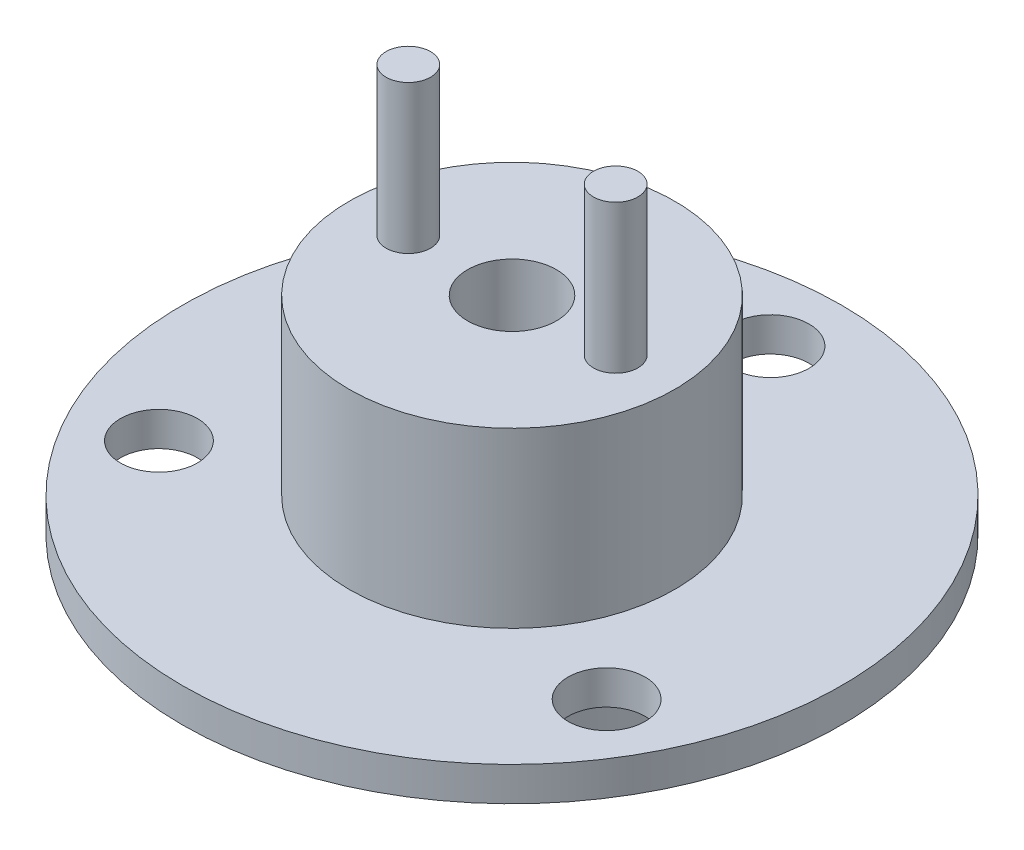
SolidWorks part; units mm, degrees
ref_plane "Alzado" through (0, 0, 0) normal (0, 0, 1) x (1, 0, 0)
ref_plane "Planta" through (0, 0, 0) normal (0, 1, 0) x (1, 0, 0)
ref_plane "Vista lateral" through (0, 0, 0) normal (1, 0, 0) x (0, 0, -1)
sketch "Croquis1" plane through (0, 0, 0) normal (0, 1, 0) x (1, 0, 0)
  circle A0 centre (0, 0) radius 11
  dimension "D1" = 22
extrude "Saliente-Extruir1" add sketch "Croquis1" along normal blind 19
ref_plane "Plano1" through (0, 5, 0) normal (0, 1, 0) x (1, 0, 0)
sketch "Croquis2" plane through (0, 5, 0) normal (0, 1, 0) x (1, 0, 0)
  circle A0 centre (0, 0) radius 22.25
  dimension "D1" = 44.5
extrude "Saliente-Extruir2" add sketch "Croquis2" along normal blind 2.3 contours A0
sketch "Croquis3" plane through (0, 5, 0) normal (0, -1, 0) x (1, 0, 0)
  line L0 (0, 0) -> (-15.1121, 8.725) construction
  line L1 (0, 0) -> (15.1121, 8.725) construction
  line L2 (0, 0) -> (0, -17.45) construction
  circle A1 centre (15.1121, 8.725) radius 2.6
  circle A2 centre (-15.1121, 8.725) radius 2.6
  circle A3 centre (0, -17.45) radius 2.6
  dimension "D4" = 5.2
  dimension "D5" = 5.2
  dimension "D6" = 5.2
  dimension "D2" = 120
  dimension "D3" = 120
extrude "Cortar-Extruir1" cut sketch "Croquis3" against normal blind 2.3
sketch "Croquis4" plane through (0, 19, 0) normal (0, 1, 0) x (1, 0, 0)
  circle A0 centre (0, 0) radius 3
  dimension "D1" = 6
extrude "Cortar-Extruir2" cut sketch "Croquis4" against normal blind 27.3 contours A0
sketch "Croquis5" plane through (0, 19, 0) normal (0, 1, 0) x (1, 0, 0)
  line L0 (-3, 0) -> (-7, 0) construction
  line L1 (-10.45, 0) -> (10.45, 0) construction
  line L2 (3, 0) -> (7, 0) construction
  circle A0 centre (0, 0) radius 3 construction
  circle A1 centre (-7, 0) radius 1.5
  circle A2 centre (7, 0) radius 1.5
  dimension "D3" = 3
  dimension "D4" = 3
  dimension "D1" = 4
  dimension "D2" = 4
extrude "Saliente-Extruir3" add sketch "Croquis5" along normal blind 10
